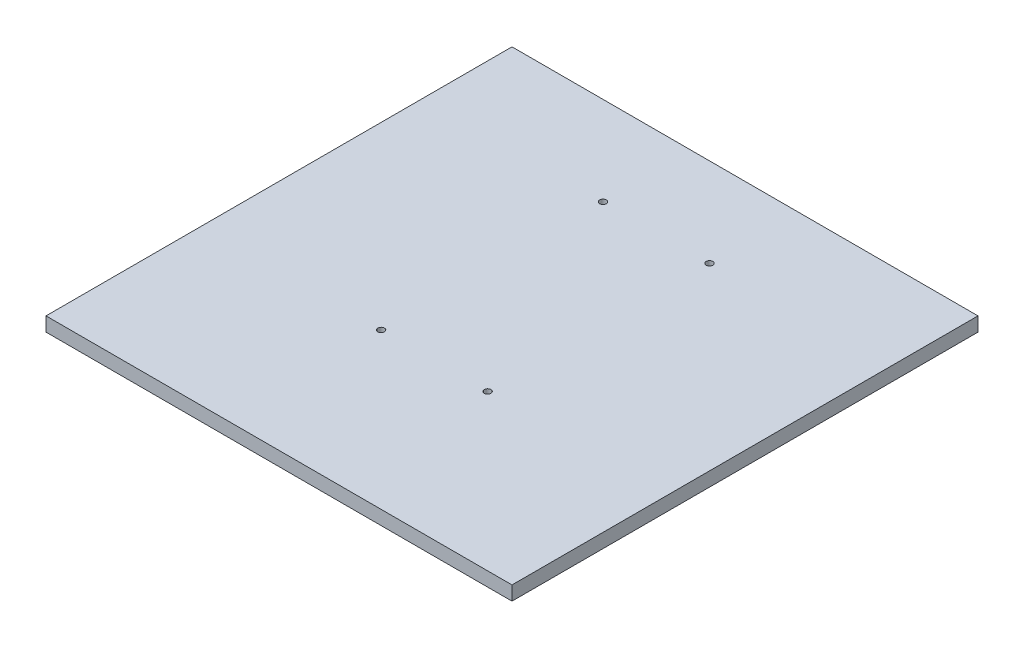
SolidWorks part; units mm, degrees
material "Balsa"
ref_plane "Front Plane" through (0, 0, 0) normal (0, 0, 1) x (1, 0, 0)
ref_plane "Top Plane" through (0, 0, 0) normal (0, 1, 0) x (1, 0, 0)
ref_plane "Right Plane" through (0, 0, 0) normal (1, 0, 0) x (0, 0, -1)
sketch "Sketch1" plane through (0, 0, 0) normal (0, 1, 0) x (1, 0, 0)
  line L1 (105, -105) -> (-105, -105)
  line L2 (105, -105) -> (105, 105)
  line L3 (105, 105) -> (-105, 105)
  line L4 (-105, -105) -> (-105, 105)
  line L5 (105, -105) -> (-105, 105) construction
  line L6 (105, 105) -> (-105, -105) construction
  point P0 (0, 0)
  dimension "D1" = 210
extrude "Boss-Extrude1" add sketch "Sketch1" along normal blind 6.35
sketch "Sketch2" plane through (0, 6.35, 0) normal (0, 1, 0) x (1, 0, 0)
  line L0 (105, 105) -> (-105, 105) construction
  line L1 (24, 65) -> (-24, 65) construction
  line L2 (24, 65) -> (24, -35) construction
  line L3 (24, -35) -> (-24, -35) construction
  line L4 (-24, 65) -> (-24, -35) construction
  line L5 (24, 65) -> (-24, -35) construction
  line L6 (24, -35) -> (-24, 65) construction
  circle A0 centre (24, -35) radius 1.5
  circle A1 centre (-24, -35) radius 1.5
  circle A2 centre (-24, 65) radius 1.5
  circle A3 centre (24, 65) radius 1.5
  point P0 (0, 15)
  dimension "D3" = 3
  dimension "D1" = 48
  dimension "D2" = 100
  dimension "D4" = 40
extrude "Cut-Extrude1" cut sketch "Sketch2" against normal through all
